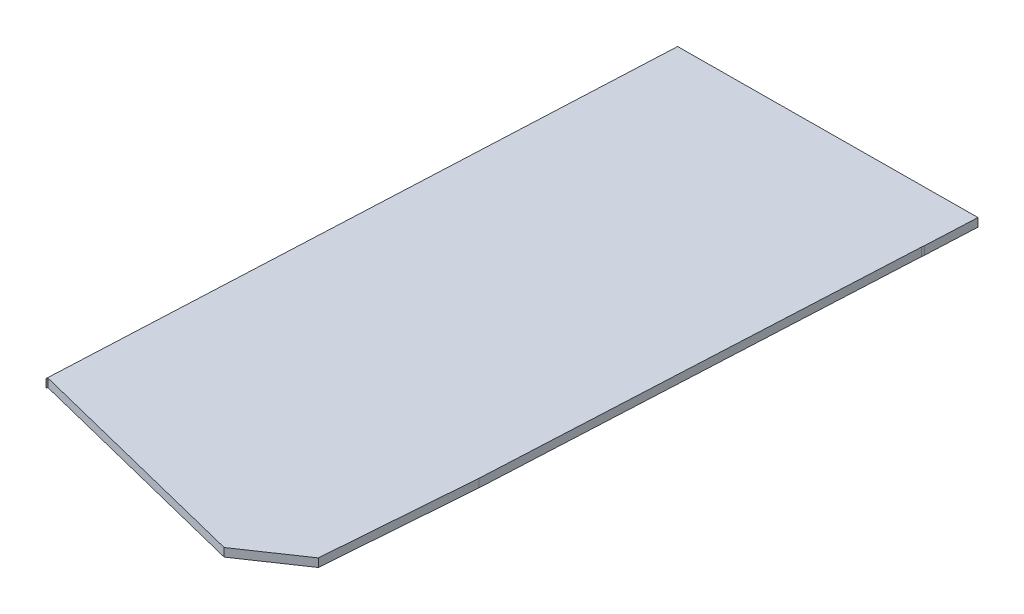
SolidWorks part; units mm, degrees
ref_plane "Plan de face" through (0, 0, 0) normal (0, 0, 1) x (1, 0, 0)
ref_plane "Plan de dessus" through (0, 0, 0) normal (0, 1, 0) x (1, 0, 0)
ref_plane "Plan de droite" through (0, 0, 0) normal (1, 0, 0) x (0, 0, -1)
sketch "Esquisse1" plane through (0, 0, 0) normal (0, 1, 0) x (1, 0, 0)
  line L0 (6.7913, 145.0656) -> (0, 0)
  line L1 (0, 0) -> (0.1071, 0.3484)
  line L2 (0.1071, 0.3484) -> (56.602, -13.7602)
  line L3 (56.602, -13.7602) -> (70.0715, -4.6023)
  line L4 (70.0715, -4.6023) -> (72.8174, 31.3197)
  line L5 (72.8174, 31.3197) -> (77.8695, 132.6767)
  line L6 (77.8695, 132.6767) -> (77.9348, 133.2377)
  line L7 (77.9348, 133.2377) -> (78.5123, 145.572)
  line L8 (78.5123, 145.572) -> (6.7913, 145.0656)
  point P9 (0, 0)
extrude "Boss.-Extru.1" add sketch "Esquisse1" along normal blind 2
